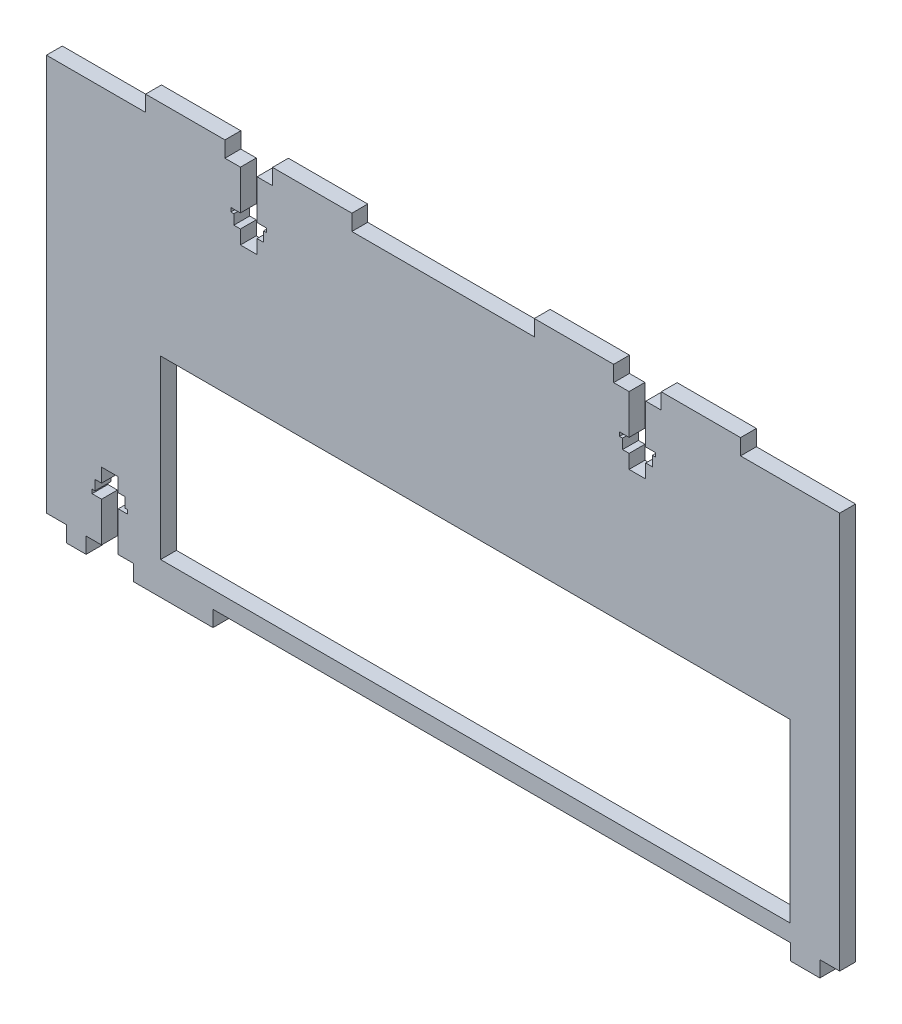
SolidWorks part; units mm, degrees
ref_plane "Front Plane" through (0, 0, 0) normal (0, 0, 1) x (1, 0, 0)
ref_plane "Top Plane" through (0, 0, 0) normal (0, 1, 0) x (1, 0, 0)
ref_plane "Right Plane" through (0, 0, 0) normal (1, 0, 0) x (0, 0, -1)
sketch "Sketch1" plane through (0, 0, 0) normal (0, 0, 1) x (1, 0, 0)
  line L0 (-55, 50) -> (-43, 50)
  line L1 (-100, 50) -> (-75, 50)
  line L2 (-100, 50) -> (-100, -50)
  line L3 (-100, -50) -> (-100, -54)
  line L4 (100, 50) -> (100, -50)
  line L5 (-100, 50) -> (100, -50) construction
  line L6 (-100, -50) -> (100, 50) construction
  line L7 (-23, 50) -> (23, 50)
  line L8 (-75, 50) -> (-75, 54)
  line L9 (-75, 54) -> (-55, 54)
  line L10 (-55, 50) -> (-55, 54)
  line L11 (43, 50) -> (55, 50)
  line L12 (-43, 50) -> (-43, 54)
  line L13 (-43, 54) -> (-23, 54)
  line L14 (-23, 50) -> (-23, 54)
  line L15 (75, 50) -> (100, 50)
  line L16 (23, 50) -> (23, 54)
  line L17 (23, 54) -> (43, 54)
  line L18 (43, 50) -> (43, 54)
  line L19 (95, -50) -> (100, -50)
  line L20 (55, 50) -> (55, 54)
  line L21 (55, 54) -> (75, 54)
  line L22 (75, 50) -> (75, 54)
  line L23 (-100, -54) -> (-90, -54)
  line L24 (-90, -54) -> (-90, -50)
  line L25 (-90, -50) -> (-78, -50)
  line L26 (-78, -50) -> (-78, -54)
  line L27 (-58, -50) -> (87.6, -50)
  line L28 (87.6, -50) -> (87.6, -54)
  line L29 (87.6, -54) -> (95, -54)
  line L30 (95, -50) -> (95, -54)
  line L31 (-78, -54) -> (-58, -54)
  line L32 (-58, -54) -> (-58, -50)
  point P0 (0, 0)
  dimension "D1" = 200
  dimension "D2" = 100
  dimension "D3" = 4
  dimension "D4" = 12
  dimension "D5" = 20
  dimension "D6" = 20
  dimension "D7" = 25
  dimension "D8" = 12
  dimension "D9" = 20
  dimension "D10" = 20
  dimension "D11" = 25
  dimension "D12" = 10
  dimension "D13" = 12
  dimension "D14" = 20
  dimension "D15" = 5
  dimension "D16" = 7.4
  dimension "D17" = 4
extrude "Boss-Extrude1" add sketch "Sketch1" along normal blind 4
sketch "Sketch2" plane through (0, 0, 0) normal (0, 0, -1) x (-1, 0, 0)
  line L0 (58, -50) -> (-87.6, -50) construction
  line L1 (-87.53, -1.29) -> (71.22, -1.29)
  line L2 (-87.53, -1.29) -> (-87.53, -45.74)
  line L3 (-87.53, -45.74) -> (71.22, -45.74)
  line L4 (71.22, -1.29) -> (71.22, -45.74)
  line L6 (-100, -50) -> (-100, 50) construction
  dimension "D1" = 158.75
  dimension "D2" = 44.45
  dimension "D3" = 4.26
  dimension "D5" = 12.47
extrude "Cut-Extrude1" cut sketch "Sketch2" against normal blind 6
sketch "Sketch3" plane through (0, 0, 0) normal (0, 0, -1) x (-1, 0, 0)
  line L0 (-51.1, 50) -> (-46.9, 50)
  line L1 (49, 50) -> (49, 33) construction
  line L2 (51.1, 50) -> (51.1, 40)
  line L3 (51.1, 33) -> (46.9, 33)
  line L4 (46.9, 50) -> (46.9, 40)
  line L5 (52.75, 36.5) -> (51.1, 36.5)
  line L6 (52.75, 36.5) -> (52.75, 39)
  line L7 (46.9, 36.5) -> (46.9, 33)
  line L8 (45.25, 36.5) -> (45.25, 39)
  line L9 (53.5, 39) -> (53.5, 40)
  line L10 (44.5, 40) -> (46.9, 40)
  line L11 (0, 0) -> (0, 50) construction
  line L12 (-23, 50) -> (23, 50) construction
  line L13 (46.9, 40) -> (44.5, 40)
  line L14 (44.5, 39) -> (44.5, 40)
  line L15 (44.5, 39) -> (45.25, 39)
  line L16 (46.9, 36.5) -> (46.9, 33)
  line L17 (45.25, 39) -> (44.5, 39)
  line L18 (51.1, 36.5) -> (52.75, 36.5)
  line L19 (52.75, 39) -> (53.5, 39)
  line L20 (46.9, 36.5) -> (45.25, 36.5)
  line L21 (51.1, 36.5) -> (51.1, 33)
  line L22 (51.1, 40) -> (53.5, 40)
  line L23 (52.75, 36.5) -> (52.75, 39)
  line L24 (81.9, -50) -> (86.1, -50)
  line L25 (81.9, -50) -> (81.9, -40)
  line L26 (81.9, -33) -> (86.1, -33)
  line L27 (86.1, -50) -> (86.1, -40)
  line L28 (84, -50) -> (84, -33) construction
  line L29 (80.25, -36.5) -> (81.9, -36.5)
  line L30 (80.25, -36.5) -> (80.25, -39)
  line L31 (86.1, -36.5) -> (86.1, -33)
  line L32 (87.75, -36.5) -> (87.75, -39)
  line L33 (79.5, -39) -> (79.5, -40)
  line L34 (88.5, -40) -> (86.1, -40)
  line L36 (86.1, -40) -> (88.5, -40)
  line L37 (88.5, -39) -> (88.5, -40)
  line L38 (88.5, -39) -> (87.75, -39)
  line L39 (86.1, -36.5) -> (86.1, -33)
  line L40 (87.75, -39) -> (88.5, -39)
  line L41 (81.9, -36.5) -> (80.25, -36.5)
  line L42 (80.25, -39) -> (79.5, -39)
  line L43 (86.1, -36.5) -> (87.75, -36.5)
  line L44 (81.9, -36.5) -> (81.9, -33)
  line L45 (81.9, -40) -> (79.5, -40)
  line L46 (80.25, -36.5) -> (80.25, -39)
  line L47 (81.9, -36.5) -> (81.9, -33)
  line L48 (79.5, -39) -> (80.25, -39)
  line L49 (79.5, -39) -> (79.5, -40)
  line L50 (79.5, -40) -> (81.9, -40)
  line L51 (88.5, -39) -> (88.5, -40)
  line L52 (87.75, -36.5) -> (87.75, -39)
  line L53 (87.75, -36.5) -> (86.1, -36.5)
  line L54 (81.9, -50) -> (81.9, -40)
  line L55 (86.1, -50) -> (86.1, -40)
  line L56 (81.9, -50) -> (81.9, -40)
  line L57 (86.1, -50) -> (86.1, -40)
  line L58 (80.25, -36.5) -> (81.9, -36.5)
  line L59 (80.25, -36.5) -> (80.25, -39)
  line L60 (79.5, -39) -> (79.5, -40)
  line L61 (88.5, -40) -> (86.1, -40)
  line L62 (88.5, -39) -> (88.5, -40)
  line L63 (88.5, -39) -> (87.75, -39)
  line L64 (86.1, -36.5) -> (86.1, -33)
  line L65 (87.75, -36.5) -> (87.75, -39)
  line L66 (86.1, -40) -> (88.5, -40)
  line L67 (86.1, -36.5) -> (86.1, -33)
  line L68 (81.9, -36.5) -> (80.25, -36.5)
  line L69 (87.75, -39) -> (88.5, -39)
  line L70 (86.1, -36.5) -> (87.75, -36.5)
  line L71 (80.25, -39) -> (79.5, -39)
  line L72 (81.9, -36.5) -> (81.9, -33)
  line L73 (79.5, -39) -> (80.25, -39)
  line L74 (79.5, -39) -> (79.5, -40)
  line L75 (81.9, -40) -> (79.5, -40)
  line L76 (79.5, -40) -> (81.9, -40)
  line L77 (88.5, -39) -> (88.5, -40)
  line L78 (80.25, -36.5) -> (80.25, -39)
  line L79 (81.9, -36.5) -> (81.9, -33)
  line L80 (87.75, -36.5) -> (87.75, -39)
  line L81 (87.75, -36.5) -> (86.1, -36.5)
  line L82 (81.9, -50) -> (81.9, -40)
  line L83 (86.1, -50) -> (86.1, -40)
  line L84 (90, -50) -> (78, -50) construction
  line L85 (51.1, 36.5) -> (51.1, 33)
  line L86 (53.5, 39) -> (52.75, 39)
  line L87 (53.5, 39) -> (53.5, 40)
  line L88 (53.5, 40) -> (51.1, 40)
  line L89 (44.5, 39) -> (44.5, 40)
  line L90 (45.25, 36.5) -> (45.25, 39)
  line L91 (45.25, 36.5) -> (46.9, 36.5)
  line L92 (51.1, 50) -> (51.1, 40)
  line L93 (46.9, 50) -> (46.9, 40)
  line L94 (51.1, 50) -> (51.1, 40)
  line L95 (46.9, 50) -> (46.9, 40)
  line L96 (52.75, 36.5) -> (51.1, 36.5)
  line L97 (52.75, 36.5) -> (52.75, 39)
  line L98 (53.5, 39) -> (53.5, 40)
  line L99 (44.5, 40) -> (46.9, 40)
  line L100 (44.5, 39) -> (44.5, 40)
  line L101 (44.5, 39) -> (45.25, 39)
  line L102 (46.9, 36.5) -> (46.9, 33)
  line L103 (45.25, 36.5) -> (45.25, 39)
  line L104 (46.9, 40) -> (44.5, 40)
  line L105 (46.9, 36.5) -> (46.9, 33)
  line L106 (51.1, 36.5) -> (52.75, 36.5)
  line L107 (45.25, 39) -> (44.5, 39)
  line L108 (46.9, 36.5) -> (45.25, 36.5)
  line L109 (52.75, 39) -> (53.5, 39)
  line L110 (51.1, 36.5) -> (51.1, 33)
  line L111 (53.5, 39) -> (52.75, 39)
  line L112 (53.5, 39) -> (53.5, 40)
  line L113 (51.1, 40) -> (53.5, 40)
  line L114 (53.5, 40) -> (51.1, 40)
  line L115 (44.5, 39) -> (44.5, 40)
  line L116 (52.75, 36.5) -> (52.75, 39)
  line L117 (51.1, 36.5) -> (51.1, 33)
  line L118 (45.25, 36.5) -> (45.25, 39)
  line L119 (45.25, 36.5) -> (46.9, 36.5)
  line L120 (51.1, 50) -> (51.1, 40)
  line L121 (46.9, 50) -> (46.9, 40)
  line L122 (51.1, 50) -> (46.9, 50)
  line L133 (-49, 50) -> (-49, 33) construction
  line L134 (-46.9, 50) -> (-46.9, 40)
  line L135 (-51.1, 50) -> (-51.1, 40)
  line L136 (-45.25, 36.5) -> (-46.9, 36.5)
  line L137 (-45.25, 36.5) -> (-45.25, 39)
  line L138 (-51.1, 36.5) -> (-51.1, 33)
  line L139 (-52.75, 36.5) -> (-52.75, 39)
  line L140 (-44.5, 39) -> (-44.5, 40)
  line L141 (-53.5, 40) -> (-51.1, 40)
  line L142 (-51.1, 40) -> (-53.5, 40)
  line L143 (-53.5, 39) -> (-53.5, 40)
  line L144 (-53.5, 39) -> (-52.75, 39)
  line L145 (-51.1, 36.5) -> (-51.1, 33)
  line L146 (-52.75, 39) -> (-53.5, 39)
  line L147 (-46.9, 36.5) -> (-45.25, 36.5)
  line L148 (-45.25, 39) -> (-44.5, 39)
  line L149 (-51.1, 36.5) -> (-52.75, 36.5)
  line L150 (-46.9, 36.5) -> (-46.9, 33)
  line L151 (-46.9, 40) -> (-44.5, 40)
  line L152 (-45.25, 36.5) -> (-45.25, 39)
  line L153 (-46.9, 36.5) -> (-46.9, 33)
  line L154 (-44.5, 39) -> (-45.25, 39)
  line L155 (-44.5, 39) -> (-44.5, 40)
  line L156 (-44.5, 40) -> (-46.9, 40)
  line L157 (-53.5, 39) -> (-53.5, 40)
  line L158 (-52.75, 36.5) -> (-52.75, 39)
  line L159 (-52.75, 36.5) -> (-51.1, 36.5)
  line L160 (-46.9, 50) -> (-46.9, 40)
  line L161 (-51.1, 50) -> (-51.1, 40)
  line L162 (-46.9, 50) -> (-46.9, 40)
  line L163 (-51.1, 50) -> (-51.1, 40)
  line L164 (-45.25, 36.5) -> (-46.9, 36.5)
  line L165 (-45.25, 36.5) -> (-45.25, 39)
  line L166 (-44.5, 39) -> (-44.5, 40)
  line L167 (-53.5, 40) -> (-51.1, 40)
  line L168 (-53.5, 39) -> (-53.5, 40)
  line L169 (-53.5, 39) -> (-52.75, 39)
  line L170 (-51.1, 36.5) -> (-51.1, 33)
  line L171 (-52.75, 36.5) -> (-52.75, 39)
  line L172 (-51.1, 40) -> (-53.5, 40)
  line L173 (-51.1, 36.5) -> (-51.1, 33)
  line L174 (-46.9, 36.5) -> (-45.25, 36.5)
  line L175 (-52.75, 39) -> (-53.5, 39)
  line L176 (-51.1, 36.5) -> (-52.75, 36.5)
  line L177 (-45.25, 39) -> (-44.5, 39)
  line L178 (-46.9, 36.5) -> (-46.9, 33)
  line L179 (-44.5, 39) -> (-45.25, 39)
  line L180 (-44.5, 39) -> (-44.5, 40)
  line L181 (-46.9, 40) -> (-44.5, 40)
  line L182 (-44.5, 40) -> (-46.9, 40)
  line L183 (-53.5, 39) -> (-53.5, 40)
  line L184 (-45.25, 36.5) -> (-45.25, 39)
  line L185 (-46.9, 36.5) -> (-46.9, 33)
  line L186 (-52.75, 36.5) -> (-52.75, 39)
  line L187 (-52.75, 36.5) -> (-51.1, 36.5)
  line L188 (-46.9, 50) -> (-46.9, 40)
  line L189 (-51.1, 33) -> (-46.9, 33)
  line L190 (-51.1, 50) -> (-51.1, 40)
  line M19 (55, 50) -> (43, 50)
  line M27 (-43, 50) -> (-55, 50)
  line M58 (78, -50) -> (90, -50)
  dimension "D5" = 4.2
  dimension "D6" = 17
  dimension "D7" = 7.5
  dimension "D8" = 2.5
  dimension "D9" = 9
  dimension "D10" = 1
  dimension "D11" = 10
extrude "Cut-Extrude2" cut sketch "Sketch3" against normal blind 10 contours L138 L189 L150 L136 L137 L148 L140 L151 L134 L135 L141 L143 L144 L139 L149 M27 | L22 L2 L4 L10 L14 L15 L8 L20 L7 L3 L21 L5 L6 L19 L9 M19 | L45 L25 L27 L34 L37 L38 L32 L43 L31 L26 L44 L29 L30 L42 L33 M58
sketch "Sketch4" plane through (0, 0, 0) normal (0, 0, -1) x (-1, 0, 0)
  line L0 (90, -50) -> (86.1, -50) construction
  line L1 (100, -54) -> (95, -54)
  line L2 (100, -54) -> (100, -50)
  line L3 (100, -50) -> (95, -50)
  line L4 (95, -54) -> (95, -50)
  dimension "D1" = 5
extrude "Cut-Extrude3" cut sketch "Sketch4" against normal blind 10
